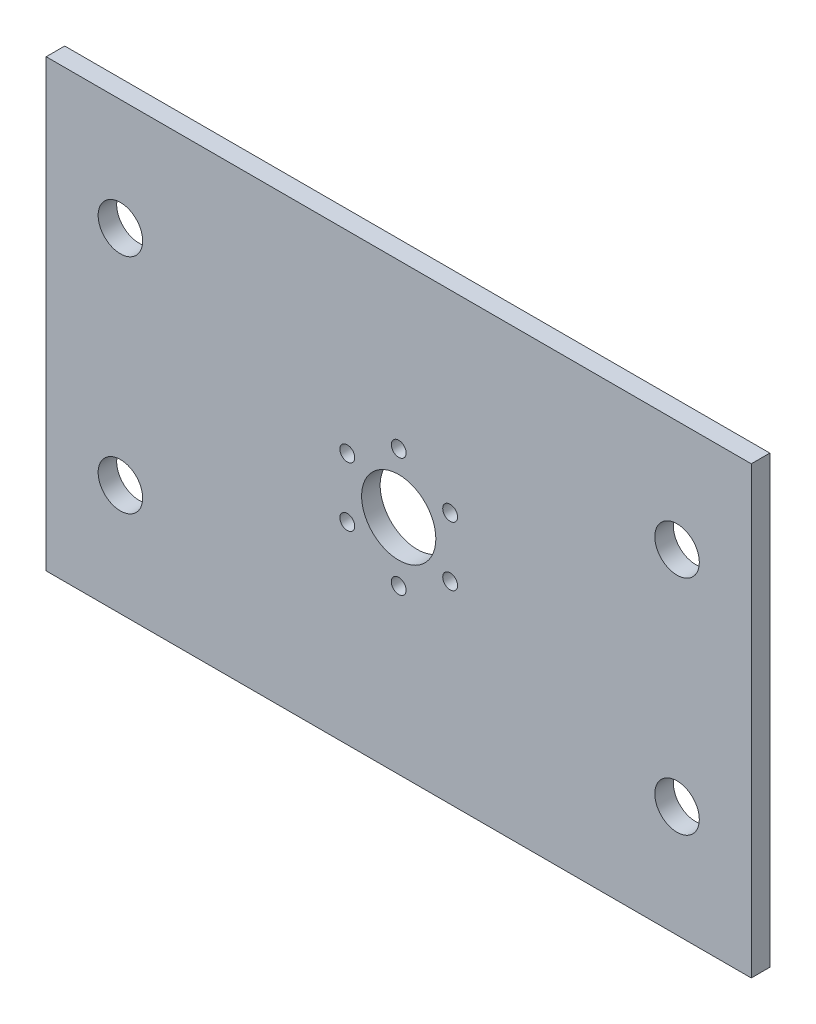
SolidWorks part; units mm, degrees
ref_plane "Front Plane" through (0, 0, 0) normal (0, 0, 1) x (1, 0, 0)
ref_plane "Top Plane" through (0, 0, 0) normal (0, 1, 0) x (1, 0, 0)
ref_plane "Right Plane" through (0, 0, 0) normal (1, 0, 0) x (0, 0, -1)
sketch "Sketch1" plane through (0, 0, 0) normal (0, 0, 1) x (1, 0, 0)
  line L1 (-95, 60) -> (95, 60)
  line L2 (-95, 60) -> (-95, -60)
  line L3 (-95, -60) -> (95, -60)
  line L4 (95, 60) -> (95, -60)
  circle A0 centre (-75, 30) radius 6
  circle A1 centre (75, 30) radius 6
  circle A2 centre (75, -30) radius 6
  circle A3 centre (-75, -30) radius 6
  circle A4 centre (0, 0) radius 10
  circle A5 centre (0, 0) radius 16 construction
  circle A6 centre (0, 16) radius 2
  circle A7 centre (13.8564, 8) radius 2
  circle A8 centre (13.8564, -8) radius 2
  circle A9 centre (0, -16) radius 2
  circle A10 centre (-13.8564, -8) radius 2
  circle A11 centre (-13.8564, 8) radius 2
  point P0 (0, 0)
  point P31 (0, 0)
  dimension "D3" = 12
  dimension "D4" = 12
  dimension "D5" = 12
  dimension "D6" = 12
  dimension "D17" = 20
  dimension "D18" = 32
  dimension "D19" = 4
  dimension "D1" = 190
  dimension "D2" = 120
  dimension "D7" = 30
  dimension "D8" = 30
  dimension "D9" = 30
  dimension "D10" = 30
  dimension "D11" = 20
  dimension "D12" = 20
  dimension "D13" = 20
  dimension "D14" = 20
  dimension "D15" = 95
  dimension "D16" = 60
  dimension "D20" = 6
extrude "Boss-Extrude1" add sketch "Sketch1" along normal blind 5
